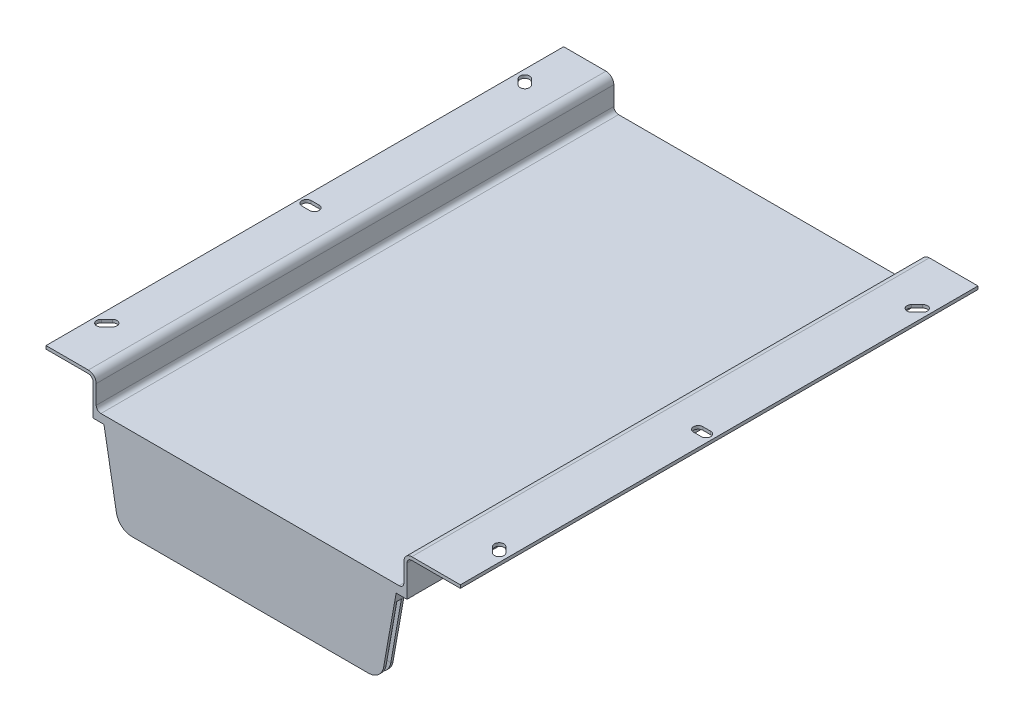
SolidWorks part; units mm, degrees
ref_plane "Plan de face" through (0, 0, 0) normal (0, 0, 1) x (1, 0, 0)
ref_plane "Plan de dessus" through (0, 0, 0) normal (0, 1, 0) x (1, 0, 0)
ref_plane "Plan de droite" through (0, 0, 0) normal (1, 0, 0) x (0, 0, -1)
sketch "Esquisse1" plane through (0, 0, 0) normal (0, 0, 1) x (1, 0, 0)
  line L3 (-107.913, 2) -> (82.2439, 2)
  line L5 (90.2439, 22) -> (116.2439, 22)
  line L7 (90.2439, 20) -> (116.2439, 20)
  line L10 (87.2439, 0) -> (-112.913, 0)
  line L11 (-137.913, 22) -> (-115.913, 22)
  line L12 (-137.913, 20) -> (-115.913, 20)
  line L17 (-10.8346, 2) -> (-10.8346, 71.8152) construction
  line L18 (116.2439, 20) -> (121.2439, 20)
  line L20 (116.2439, 22) -> (121.2439, 22)
  line L21 (121.2439, 20) -> (121.2439, 22)
  line L22 (-137.913, 20) -> (-142.913, 20)
  line L24 (-137.913, 22) -> (-142.913, 22)
  line L25 (-142.913, 20) -> (-142.913, 22)
  line L26 (87.2439, 17) -> (87.2439, 0)
  line L27 (85.2439, 5) -> (85.2439, 17)
  line L28 (-112.913, 17) -> (-112.913, 0)
  line L29 (-110.913, 5) -> (-110.913, 17)
  arc A23 (85.2439, 17) -> (90.2439, 22) centre (90.2439, 17) cw
  arc A24 (-115.913, 22) -> (-110.913, 17) centre (-115.913, 17) cw
  arc A25 (-115.913, 20) -> (-112.913, 17) centre (-115.913, 17) cw
  arc A26 (90.2439, 20) -> (87.2439, 17) centre (90.2439, 17) ccw
  arc A27 (-110.913, 5) -> (-107.913, 2) centre (-107.913, 5) ccw
  arc A28 (85.2439, 5) -> (82.2439, 2) centre (82.2439, 5) cw
  dimension "D9" = 3
  dimension "D10" = 5
  dimension "D7" = 3
  dimension "D6" = 5
  dimension "D3" = 2
  dimension "D4" = 2
  dimension "D5" = 2
  dimension "D8" = 2
  dimension "D19" = 2
  dimension "D20" = 2
  dimension "D22" = 20
  dimension "D23" = 20
  dimension "D24" = 5
  dimension "D25" = 5
extrude "Boss.-Extru.1" add sketch "Esquisse1" along normal blind 320 and the other way blind 10
sketch "Esquisse2" plane through (0, 20, 0) normal (0, -1, 0) x (1, 0, 0)
  line L0 (111.2439, 158.4034) -> (-163.1947, 158.4034) construction
  line L1 (90.2439, -10) -> (121.2439, -10) construction
  line L2 (90.2439, 320) -> (121.2439, 320) construction
  line L3 (-142.913, 320) -> (-115.913, 320) construction
  line L4 (-138.413, 158.4034) -> (-133.413, 158.4034) construction
  line L5 (-142.913, -10) -> (-115.913, -10) construction
  line L6 (-137.663, 20) -> (-134.163, 23.5) construction
  line L7 (-139.7843, 22.1213) -> (-136.2843, 25.6213)
  line L8 (-135.5417, 17.8787) -> (-132.0417, 21.3787)
  line L9 (-134.163, 286.5) -> (-137.663, 290) construction
  line L10 (-136.2843, 284.3787) -> (-139.7843, 287.8787)
  line L11 (-132.0417, 288.6213) -> (-135.5417, 292.1213)
  line L12 (115.9939, 290) -> (112.4939, 286.5) construction
  line L13 (118.1152, 287.8787) -> (114.6152, 284.3787)
  line L14 (113.8725, 292.1213) -> (110.3725, 288.6213)
  line L15 (112.4939, 23.5) -> (115.9939, 20) construction
  line L18 (114.6152, 25.6213) -> (118.1152, 22.1213)
  line L19 (110.3725, 21.3787) -> (113.8725, 17.8787)
  line L20 (121.2439, -10) -> (121.2439, 320) construction
  line L21 (-142.913, -10) -> (-142.913, 320) construction
  line L28 (116.2439, 158.4034) -> (111.2439, 158.4034) construction
  line L29 (116.2439, 155.4034) -> (111.2439, 155.4034)
  line L30 (116.2439, 161.4034) -> (111.2439, 161.4034)
  line L33 (-138.413, 142.4665) -> (-138.413, 177.2622) construction
  line L34 (-138.413, 161.4034) -> (-133.413, 161.4034)
  line L35 (-138.413, 155.4034) -> (-133.413, 155.4034)
  arc A8 (-139.7843, 22.1213) -> (-135.5417, 17.8787) centre (-137.663, 20) ccw
  arc A9 (-132.0417, 21.3787) -> (-136.2843, 25.6213) centre (-134.163, 23.5) ccw
  arc A10 (-136.2843, 284.3787) -> (-132.0417, 288.6213) centre (-134.163, 286.5) ccw
  arc A11 (-135.5417, 292.1213) -> (-139.7843, 287.8787) centre (-137.663, 290) ccw
  arc A12 (118.1152, 287.8787) -> (113.8725, 292.1213) centre (115.9939, 290) ccw
  arc A13 (110.3725, 288.6213) -> (114.6152, 284.3787) centre (112.4939, 286.5) ccw
  arc A18 (114.6152, 25.6213) -> (110.3725, 21.3787) centre (112.4939, 23.5) ccw
  arc A19 (113.8725, 17.8787) -> (118.1152, 22.1213) centre (115.9939, 20) ccw
  arc A24 (116.2439, 155.4034) -> (116.2439, 161.4034) centre (116.2439, 158.4034) ccw
  arc A25 (111.2439, 161.4034) -> (111.2439, 155.4034) centre (111.2439, 158.4034) ccw
  arc A26 (-138.413, 161.4034) -> (-138.413, 155.4034) centre (-138.413, 158.4034) ccw
  arc A27 (-133.413, 155.4034) -> (-133.413, 161.4034) centre (-133.413, 158.4034) ccw
  point P0 (114.2439, 21.75)
  point P13 (-135.913, 288.25)
  point P19 (114.2439, 288.25)
  point P24 (-135.913, 21.75)
  point P41 (-135.913, 158.4034)
  point P56 (113.7439, 158.4034)
  dimension "D3" = 6
  dimension "D7" = 30
  dimension "D8" = 3.5
  dimension "D14" = 3.5
  dimension "D18" = 5.25
  dimension "D20" = 5.25
  dimension "D22" = 4.5
  dimension "D25" = 6
  dimension "D4" = 6
  dimension "D5" = 6
  dimension "D6" = 6
  dimension "D9" = 3.5
  dimension "D10" = 3.5
  dimension "D11" = 30
  dimension "D12" = 5.25
  dimension "D13" = 30
  dimension "D15" = 5.25
  dimension "D16" = 3.5
  dimension "D17" = 3.5
  dimension "D19" = 30
  dimension "D21" = 5
  dimension "D23" = 3.5
  dimension "D24" = 3.5
  dimension "D26" = 5
  dimension "D27" = 7.5
  dimension "D28" = 6
extrude "Enlèv. mat.-Extru.1" cut sketch "Esquisse2" against normal blind 300
sketch "Esquisse3" plane through (0, 0, 0) normal (0, -1, 0) x (-1, 0, 0)
  line L3 (-85.2439, -314) -> (110.913, -314)
  line L4 (110.913, -320) -> (110.913, -314)
  line L5 (142.913, 10) -> (142.913, -320) construction
  line L7 (110.913, -320) -> (-85.2439, -320)
  line L11 (112.913, 10) -> (112.913, -320) construction
  line L12 (-85.2439, -314) -> (-85.2439, -320)
  dimension "D1" = 6
  dimension "D2" = 2
  dimension "D3" = 32
extrude "Boss.-Extru.2" add sketch "Esquisse3" along normal blind 56.1
sketch "Esquisse41" plane through (0, 0, 0) normal (0, -1, 0) x (1, 0, 0)
  line L14 (-110.913, 314) -> (85.2439, 314) construction
  line L15 (81.2439, 314) -> (-106.913, 314)
  line L16 (81.2439, 314) -> (81.2439, 6)
  line L17 (71.2439, -4) -> (-96.913, -4)
  line L18 (-106.913, 314) -> (-106.913, 6)
  line L19 (-112.913, -10) -> (87.2439, -10) construction
  line L20 (87.2439, -10) -> (87.2439, 320) construction
  line L21 (-112.913, -10) -> (-112.913, 320) construction
  line L23 (87.2439, -10) -> (-112.913, -10)
  line L24 (87.2439, -10) -> (87.2439, 320)
  line L25 (87.2439, 320) -> (-112.913, 320)
  line L26 (-112.913, -10) -> (-112.913, 320)
  arc A4 (-106.913, 6) -> (-96.913, -4) centre (-96.913, 6) ccw
  arc A5 (81.2439, 6) -> (71.2439, -4) centre (71.2439, 6) cw
  dimension "D2" = 6
  dimension "D4" = 10
  dimension "D1" = 6
  dimension "D3" = 6
extrude "Boss.-Extru.9" add sketch "Esquisse41" along normal blind 3
sketch "Esquisse24" plane through (0, 0, 320) normal (0, 0, 1) x (1, 0, 0)
  line L0 (80.2639, -3) -> (69.2139, -65.6863)
  line L2 (-105.9345, -3) -> (-94.8812, -65.6863)
  line L10 (85.2439, -3) -> (85.2439, -65.6863)
  line L13 (85.2439, -3) -> (80.2639, -3)
  line L14 (85.2439, -56.1) -> (-110.913, -56.1) construction
  line L20 (85.2439, -65.6863) -> (69.2139, -65.6863)
  line L22 (-94.8812, -65.6863) -> (-110.913, -65.6863)
  line L23 (-105.9345, -3) -> (-110.913, -3)
  line L24 (-110.913, -3) -> (-110.913, -65.6863)
  dimension "D1" = 16.03
  dimension "D2" = 62.6863
  dimension "D3" = 16.0318
  dimension "D4" = 4.98
  dimension "D5" = 99.997
  dimension "D6" = 100
extrude "Enlèv. mat.-Extru.22" cut sketch "Esquisse24" against normal blind 6
fillet "Congé8" radius 10 2 edges at (-96.5715, -56.1, 317) (70.9037, -56.1, 317)
fillet "Congé7" radius 0.2 1 edges at (-142.913, 21, -10)
sketch "Esquisse43" plane through (0, -3, 0) normal (0, -1, 0) x (1, 0, 0)
  line L1 (87.2439, 320) -> (80.2639, 320)
  line L2 (87.2439, 320) -> (87.2439, 315)
  line L3 (87.2439, 315) -> (80.2639, 315)
  line L5 (80.2639, 315) -> (80.2639, 320)
  line L6 (80.2639, 314) -> (80.2639, 320) construction
sketch "Esquisse44" plane through (78.3579, -13.8125, 0) normal (0.9848, -0.1736, 0) x (0, 0, -1)
  line L0 (-320, 10.9792) -> (-320, -34.548) construction
  line L1 (-320, 10.9738) -> (-314, 10.9738)
  line L2 (-320, 10.9738) -> (-320, 4.9738)
  line L3 (-320, 4.9738) -> (-314, 4.9738)
  line L4 (-314, 10.9738) -> (-314, 4.9738)
  line L5 (-314, 10.9792) -> (-314, -34.548) construction
  dimension "D1" = 6
extrude "Boss.-Extru.10" add sketch "Esquisse43" along normal blind 0.05
extrude "Boss.-Extru.11" add sketch "Esquisse44" along normal blind 0.05
sketch "Esquisse45" plane through (0, -3, 0) normal (0, -1, 0) x (1, 0, 0)
  line L1 (-105.9345, 314) -> (-112.913, 314)
  line L2 (-105.9345, 314) -> (-105.9345, 320)
  line L3 (-105.9345, 320) -> (-112.913, 320)
  line L4 (-112.913, 314) -> (-112.913, 320)
extrude "Boss.-Extru.12" add sketch "Esquisse45" along normal blind 0.05
sketch "Esquisse46" plane through (-103.2532, -18.2063, 0) normal (-0.9848, -0.1736, 0) x (0, 0, 1)
  line L0 (320, -30.0872) -> (320, 15.4409) construction
  line L1 (320, 15.4409) -> (314, 15.4409)
  line L2 (320, 15.4409) -> (320, 9.4409)
  line L3 (320, 9.4409) -> (314, 9.4409)
  line L4 (314, 15.4409) -> (314, 9.4409)
  line L5 (314, 15.4409) -> (320, 15.4409) construction
  line L6 (314, -30.0872) -> (314, 15.4409) construction
  dimension "D1" = 6
extrude "Boss.-Extru.13" add sketch "Esquisse46" along normal blind 0.05
sketch "Esquisse47" plane through (0, -3, 0) normal (0, -1, 0) x (1, 0, 0)
  line L0 (84.2439, 298.4605) -> (84.2439, 5)
  line L1 (81.2439, 6) -> (81.2439, 314) construction
  line L2 (-109.913, 298.4605) -> (-109.913, 5)
  line L3 (-106.913, 314) -> (-106.913, 6) construction
  line L4 (72.2439, -7) -> (-97.913, -7)
  line L5 (-112.913, -10) -> (87.2439, -10) construction
  arc A0 (72.2439, -7) -> (84.2439, 5) centre (72.2439, 5) ccw
  arc A1 (-97.913, -7) -> (-109.913, 5) centre (-97.913, 5) cw
  dimension "D4" = 12
  dimension "D1" = 3
  dimension "D2" = 3
  dimension "D3" = 3
sketch3d "Esquisse3D1"
  line L0 (87.2439, -3, -10) -> (87.2439, 17, -10) construction
  line L1 (-48.7981, -0.9375, -5.5) -> (-48.7981, -3.3375, -5.5)
  line L2 (-48.7981, -0.9375, -5.5) -> (-48.7981, -0.9375, -8.5)
  line L3 (-48.7981, -0.9375, -8.5) -> (-48.7981, -3.3375, -8.5)
  line L4 (-48.7981, -3.3375, -5.5) -> (-48.7981, -3.3375, -8.5)
  dimension "D2" = 136.0502
  dimension "D1" = 2.4
  dimension "D3" = 1.5
  dimension "D4" = 3
sweep "Enlèvement de matière-Balayage1" cut profiles "Esquisse3D1" path "Esquisse47"
sketch "Esquisse48" plane through (0, 0, 0) normal (1, 0, 0) x (0, 0, -1)
  line L1 (-318.5, -56.7) -> (-315.5, -56.7)
  line L2 (-318.5, -56.7) -> (-318.5, -53.7)
  line L3 (-318.5, -53.7) -> (-315.5, -53.7)
  line L4 (-315.5, -56.7) -> (-315.5, -53.7)
  dimension "D1" = 1.5
  dimension "D2" = 3
  dimension "D3" = 3
sketch "Esquisse50" plane through (0, 0, 314) normal (0, 0, -1) x (-1, 0, 0)
  line L0 (87.3922, -52.1) -> (-61.6731, -52.1)
  line L1 (-68.5668, -46.3152) -> (-76.731, 0)
  line L4 (102.4525, 0) -> (94.2859, -46.3155)
  line L5 (88.1805, -56.1) -> (-62.5123, -56.1) construction
  line L6 (98.0286, -47.8365) -> (104.8926, -8.9088) construction
  line L7 (-79.2213, -8.9142) -> (-72.3604, -47.836) construction
  line L8 (-76.731, 0) -> (102.4525, 0)
  arc A0 (-68.5668, -46.3152) -> (-61.6731, -52.1) centre (-61.6731, -45.1) ccw
  arc A1 (94.2859, -46.3155) -> (87.3922, -52.1) centre (87.3922, -45.1) cw
  dimension "D4" = 7
  dimension "D1" = 4
  dimension "D2" = 4
  dimension "D3" = 4
extrude "Enlèv. mat.-Extru.23" cut sketch "Esquisse50" against normal blind 3.5
fillet "Congé11" radius 2.5 5 edges at (72.6489, -23.1576, 317.5) (66.1728, -50.4622, 317.5) (-12.8595, -52.1, 317.5) (-91.8917, -50.4623, 317.5) (-98.3692, -23.1578, 317.5)
sketch3d "Esquisse3D4"
  line L0 (-8.2846, -56.1, 317) -> (-88.1805, -56.1, 317)
  line L1 (62.5123, -56.1, 320) -> (-88.1805, -56.1, 320) construction
  line L4 (-8.2846, -56.1, 317) -> (62.5102, -56.1, 317)
  line L6 (79.2213, -8.9142, 317) -> (72.3583, -47.8365, 317)
  line L7 (79.2213, -8.9142, 320) -> (79.2213, -8.9142, 314) construction
  line L8 (-104.8926, -8.9088, 317) -> (-98.0286, -47.8365, 317)
  line L9 (-104.8926, -8.9088, 314) -> (-104.8926, -8.9088, 320) construction
  arc A0 (-98.0286, -47.8365, 317) -> (-88.1805, -56.1, 317) centre (-88.1805, -46.1, 317) ccw
  arc A1 (72.3583, -47.8365, 317) -> (62.5102, -56.1, 317) centre (62.5102, -46.1, 317) ccw
  point P5 (-96.5715, -56.1, 317)
  point P7 (-88.1805, -46.1, 327)
  point P17 (70.9012, -56.1, 317)
  point P18 (62.5102, -46.1, 307)
  dimension "D4" = 10
  dimension "D1" = 3
  dimension "D2" = 100
  dimension "D3" = 100
sweep "Enlèvement de matière-Balayage2" cut profiles "Esquisse48" path "Esquisse3D4"
